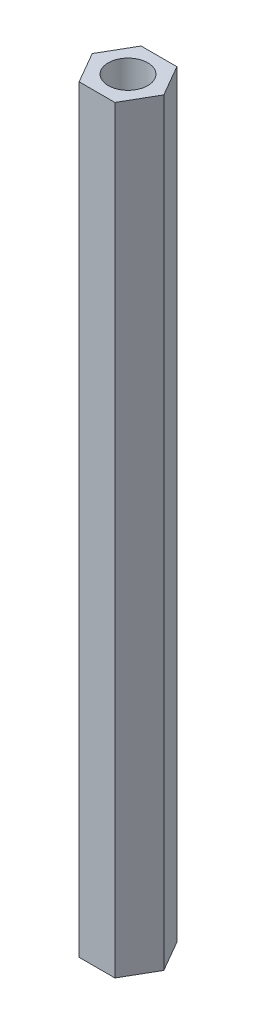
SolidWorks part; units mm, degrees
ref_plane "Front Plane" through (0, 0, 0) normal (0, 0, 1) x (1, 0, 0)
ref_plane "Top Plane" through (0, 0, 0) normal (0, 1, 0) x (1, 0, 0)
ref_plane "Right Plane" through (0, 0, 0) normal (1, 0, 0) x (0, 0, -1)
sketch "Sketch2" plane through (0, 0, 0) normal (0, 1, 0) x (1, 0, 0)
  line L1 (2.7135, 0) -> (1.3568, 2.35)
  line L2 (1.3568, 2.35) -> (-1.3568, 2.35)
  line L3 (-1.3568, 2.35) -> (-2.7135, 0)
  line L4 (-2.7135, 0) -> (-1.3568, -2.35)
  line L5 (-1.3568, -2.35) -> (1.3568, -2.35)
  line L6 (1.3568, -2.35) -> (2.7135, 0)
  circle A0 centre (0, 0) radius 2.35 construction
  circle A1 centre (0, 0) radius 1.5
  dimension "D1" = 4.7
  dimension "D3" = 3
  dimension "D2" = 2.35
extrude "Boss-Extrude1" add sketch "Sketch2" along normal blind 57.5
